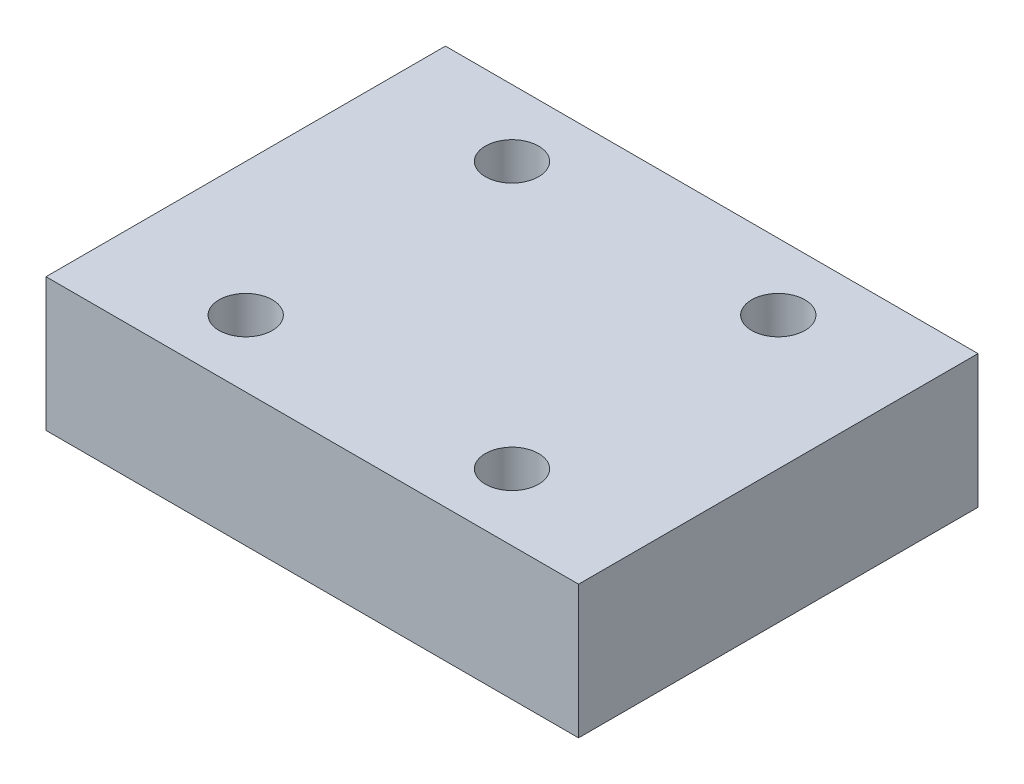
SolidWorks part; units mm, degrees
ref_plane "Front Plane" through (0, 0, 0) normal (0, 0, 1) x (1, 0, 0)
ref_plane "Top Plane" through (0, 0, 0) normal (0, 1, 0) x (1, 0, 0)
ref_plane "Right Plane" through (0, 0, 0) normal (1, 0, 0) x (0, 0, -1)
sketch "Sketch1" plane through (0, 0, 0) normal (0, 1, 0) x (1, 0, 0)
  line L1 (20, -15) -> (-20, -15)
  line L2 (20, -15) -> (20, 15)
  line L3 (20, 15) -> (-20, 15)
  line L4 (-20, -15) -> (-20, 15)
  line L5 (20, -15) -> (-20, 15) construction
  line L6 (20, 15) -> (-20, -15) construction
  point P0 (0, 0)
  dimension "D1" = 30
  dimension "D2" = 40
extrude "Boss-Extrude1" add sketch "Sketch1" along normal blind 10
sketch "Sketch2" plane through (0, 10, 0) normal (0, 1, 0) x (1, 0, 0)
  line L0 (0, -5.5) -> (0, 5.5) construction
  line L1 (-5.5, 0) -> (5.5, 0) construction
  circle A0 centre (-10, 10) radius 2
  circle A1 centre (10, 10) radius 2
  circle A2 centre (10, -10) radius 2
  circle A3 centre (-10, -10) radius 2
  dimension "D1" = 10
  dimension "D2" = 10
extrude "Cut-Extrude1" cut sketch "Sketch2" against normal blind 16
